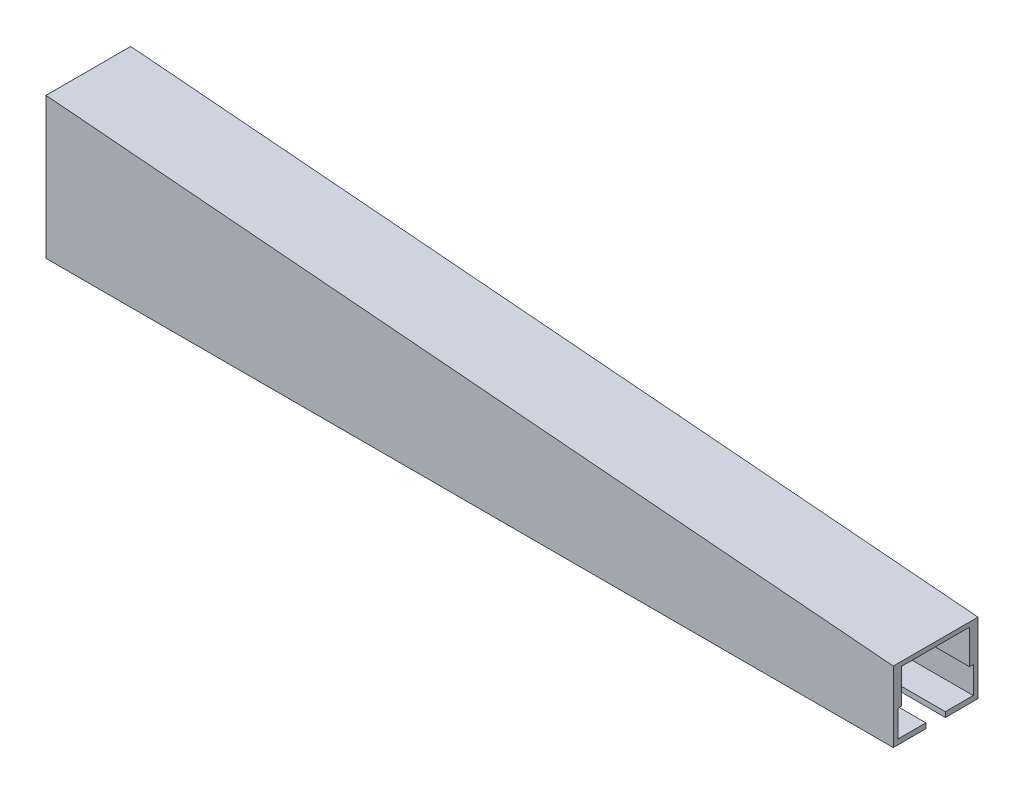
SolidWorks part; units mm, degrees
ref_plane "Спереди" through (0, 0, 0) normal (0, 0, 1) x (1, 0, 0)
ref_plane "Сверху" through (0, 0, 0) normal (0, 1, 0) x (1, 0, 0)
ref_plane "Справа" through (0, 0, 0) normal (1, 0, 0) x (0, 0, -1)
sketch "Эскиз1" plane through (0, 0, 0) normal (0, 0, 1) x (1, 0, 0)
  line L0 (0, 0) -> (300, 0)
  line L1 (300, 0) -> (300, 25)
  line L2 (300, 25) -> (0, 50)
  line L3 (0, 50) -> (0, 0)
  point P3 (0, 0)
extrude "Бобышка-Вытянуть1" add sketch "Эскиз1" along normal blind 30
sketch "Эскиз2" plane through (300, 0, 0) normal (1, 0, 0) x (0, 0, -1)
  line L0 (-18.4296, 0) -> (-18.4296, 1.7977)
  line L1 (-30, 0) -> (0, 0) construction
  line L2 (-18.4296, 1.7977) -> (-28.3234, 1.7977)
  line L3 (-28.3234, 1.7977) -> (-28.3234, 11.2975)
  line L4 (-28.3234, 11.2975) -> (-1.6766, 11.2975)
  line L5 (-18.4296, 0) -> (-11.5704, 0)
  line L6 (-15, 15.6315) -> (-15, -2.6239) construction
  line L7 (-1.6766, 1.7977) -> (-1.6766, 11.2975)
  line L8 (-11.5704, 0) -> (-11.5704, 1.7977)
  line L9 (-11.5704, 1.7977) -> (-1.6766, 1.7977)
  point P11 (-15, 11.2975)
  point P14 (-15, 0)
extrude "Вырез-Вытянуть1" cut sketch "Эскиз2" against normal through all
ref_plane "Плоскость4" through (0, 0, 15) normal (0, 0, -1) x (-1, 0, 0)
sketch "Эскиз3" plane through (0, 0, 15) normal (0, 0, -1) x (-1, 0, 0)
  line L0 (-300, 7.8084) -> (0, 7.8084)
  line L1 (-300, 0) -> (-300, 25) construction
  line L2 (0, 50) -> (0, 0) construction
  line L3 (0, 7.8084) -> (0, 47.55)
  line L4 (0, 47.55) -> (-300, 23.4371)
  line L5 (-300, 23.4371) -> (-300, 7.8084)
extrude "Вырез-Вытянуть2" cut sketch "Эскиз3" against normal blind 12 and the other way blind 12
